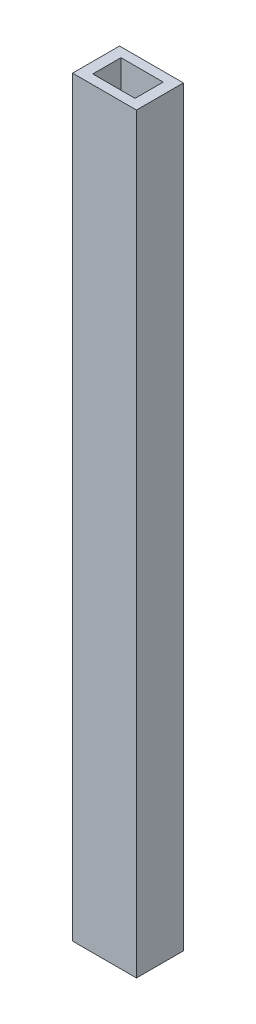
SolidWorks part; units mm, degrees
ref_plane "Front Plane" through (0, 0, 0) normal (0, 0, 1) x (1, 0, 0)
ref_plane "Top Plane" through (0, 0, 0) normal (0, 1, 0) x (1, 0, 0)
ref_plane "Right Plane" through (0, 0, 0) normal (1, 0, 0) x (0, 0, -1)
sketch "Sketch1" plane through (0, 0, 0) normal (0, 1, 0) x (1, 0, 0)
  line L1 (0, 0) -> (17.272, 0)
  line L2 (0, 0) -> (0, 12.7)
  line L3 (0, 12.7) -> (17.272, 12.7)
  line L4 (17.272, 0) -> (17.272, 12.7)
  line L5 (2.921, 10.16) -> (14.351, 10.16)
  line L6 (2.921, 10.16) -> (2.921, 2.54)
  line L7 (2.921, 2.54) -> (14.351, 2.54)
  line L8 (14.351, 10.16) -> (14.351, 2.54)
  dimension "D1" = 17.272
  dimension "D2" = 12.7
  dimension "D3" = 11.43
  dimension "D4" = 7.62
  dimension "D5" = 2.54
  dimension "D6" = 2.921
extrude "Boss-Extrude1" add sketch "Sketch1" along normal blind 203.2
equation "\"D5@Sketch1\"=(.1)"
